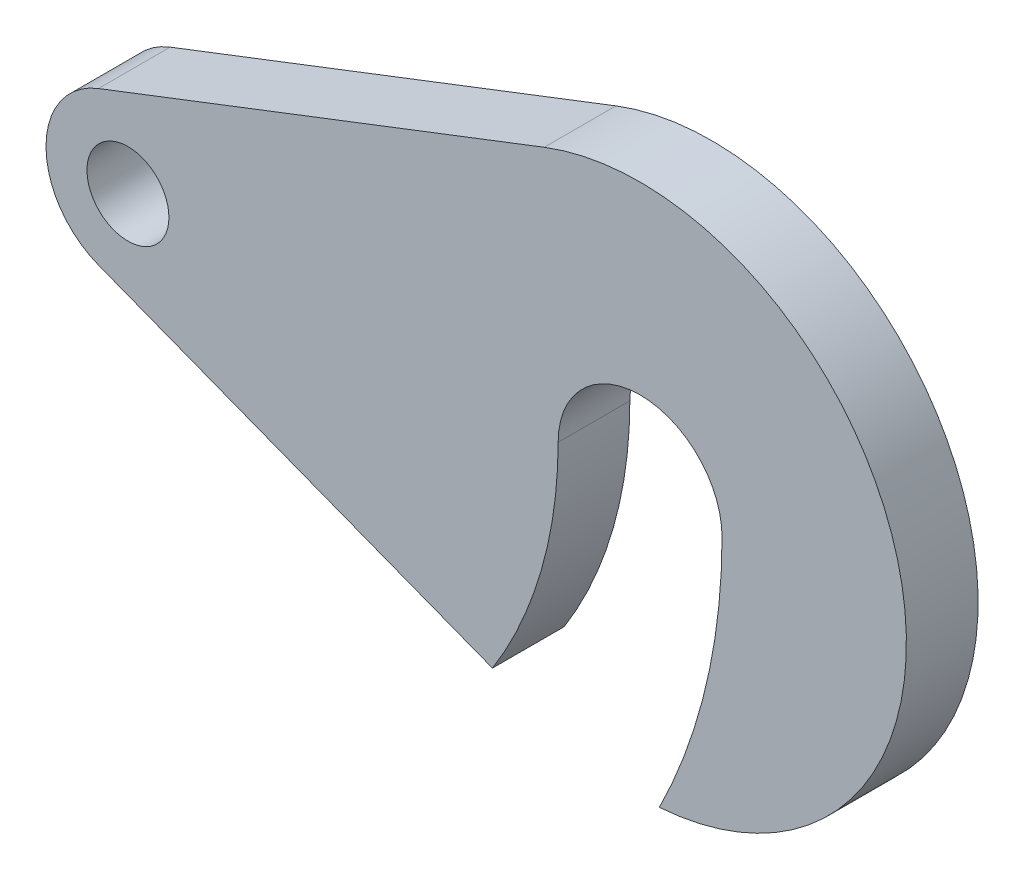
SolidWorks part; units mm, degrees
ref_plane "Přední rovina" through (0, 0, 0) normal (0, 0, 1) x (1, 0, 0)
ref_plane "Vrchní rovina" through (0, 0, 0) normal (0, 1, 0) x (1, 0, 0)
ref_plane "Pravá rovina" through (0, 0, 0) normal (1, 0, 0) x (0, 0, -1)
sketch "Skica2" plane through (0, 0, 0) normal (0, 0, 1) x (1, 0, 0)
  line L0 (-50, 0) -> (67.969, 0) construction
  line L1 (0, 0) -> (0, 59.8502) construction
  line L2 (-50, 0) -> (-50, 68.8017) construction
  line L3 (-52.88, 7.4636) -> (-9.36, 24.2568)
  line L4 (-52.88, -7.4636) -> (-14.4134, -22.3068)
  arc A0 (0, 0) -> (-12.8027, -33.412) centre (-50, 0) cw construction
  circle A1 centre (-50, 0) radius 4
  arc A2 (1.88, -25.9319) -> (-9.36, 24.2568) centre (0, 0) ccw
  arc A3 (8, 0) -> (-8, 0) centre (0, 0) ccw
  arc A4 (-52.88, 7.4636) -> (-52.88, -7.4636) centre (-50, 0) ccw
  arc A5 (-8, 0) -> (-14.4134, -22.3068) centre (-50, 0) cw
  arc A6 (8, 0) -> (1.88, -25.9319) centre (-50, 0) cw
  point P20 (0, 0)
  point P21 (0, 0)
  dimension "D1" = 50
  dimension "D2" = 8
  dimension "D3" = 26
  dimension "D4" = 8
  dimension "D5" = 8
extrude "Přidat vysunutím1" add sketch "Skica2" along normal blind 7
